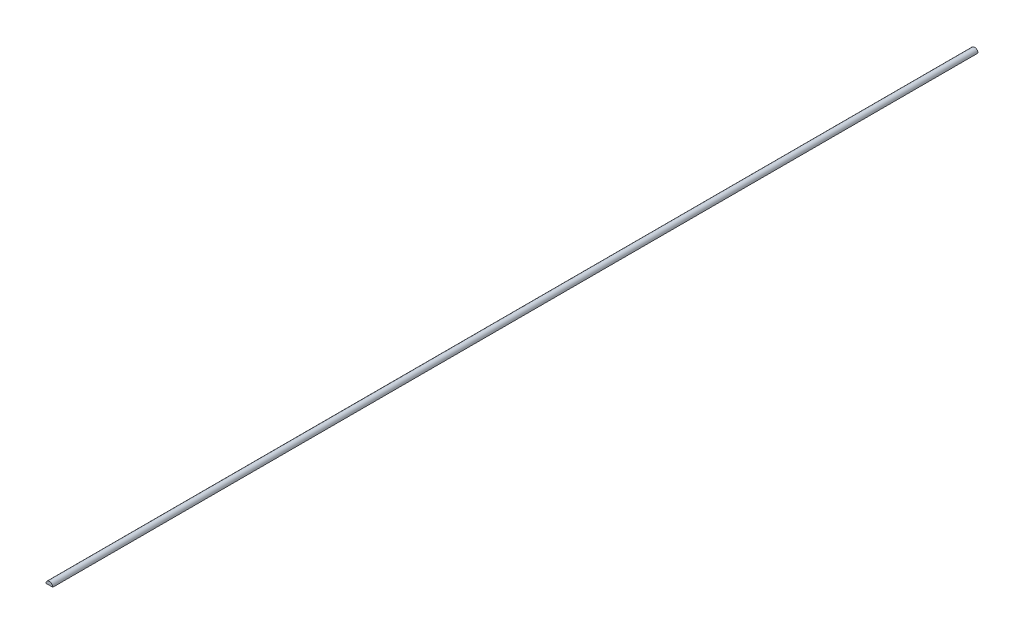
SolidWorks part; units mm, degrees
material "Acrylic (Medium-high impact)"
ref_plane "Front" through (0, 0, 0) normal (0, 0, 1) x (1, 0, 0)
ref_plane "Top" through (0, 0, 0) normal (0, 1, 0) x (1, 0, 0)
ref_plane "Right" through (0, 0, 0) normal (1, 0, 0) x (0, 0, -1)
sketch "Sketch1" plane through (0, 0, 0) normal (0, 0, 1) x (1, 0, 0)
  line L0 (-0.75, 0) -> (0.75, 0)
  arc A0 (0.75, 0) -> (-0.75, 0) centre (0, 0) ccw
  dimension "D1" = 0.75
extrude "Extrude1" add sketch "Sketch1" along normal mid plane 203.9
